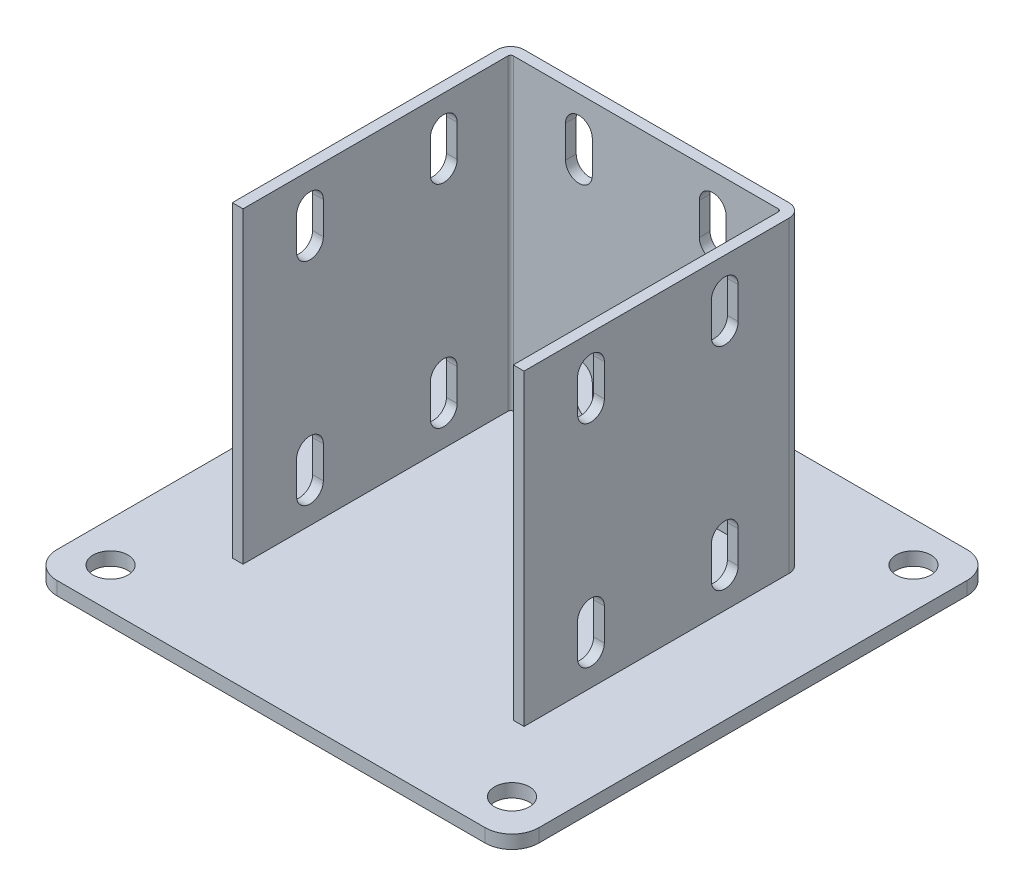
SolidWorks part; units mm, degrees
material "Ст3пс ГОСТ 380-2005"
ref_plane "Спереди" through (0, 0, 0) normal (0, 0, 1) x (1, 0, 0)
ref_plane "Сверху" through (0, 0, 0) normal (0, 1, 0) x (1, 0, 0)
ref_plane "Справа" through (0, 0, 0) normal (1, 0, 0) x (0, 0, -1)
sketch "Эскиз2" plane through (0, 0, 0) normal (0, 1, 0) x (1, 0, 0)
  line L1 (-90, -90) -> (90, -90)
  line L2 (-90, -90) -> (-90, 90)
  line L3 (-90, 90) -> (90, 90)
  line L4 (90, -90) -> (90, 90)
  line L5 (-90, -90) -> (90, 90) construction
  line L6 (-90, 90) -> (90, -90) construction
  point P0 (0, 0)
  dimension "D2" = 180
extrude "Бобышка-Вытянуть1" add sketch "Эскиз2" along normal blind 5
sketch "Эскиз3" plane through (0, 5, 0) normal (0, 1, 0) x (1, 0, 0)
  line L0 (-50.5, -50) -> (-50.5, 50)
  line L1 (-50.5, 50) -> (50.5, 50)
  line L2 (50.5, 50) -> (50.5, -50)
  point P2 (0, 50)
  point P5 (-50.5, 0)
  dimension "D2" = 101
  dimension "D3" = 100
extrude "Вытянуть-Тонкостенный1" add sketch "Эскиз3" along normal offset from surface (115 mm away) 120 thin up to face at (0, 0, 0) thin type one direction reverse wall 4
sketch "Эскиз4" plane through (0, 0, 0) normal (1, 0, 0) x (0, 0, -1)
  line L0 (54, 58.6936) -> (85, 5)
  line L1 (54, 120) -> (54, 5) construction
  line L2 (-90, 5) -> (90, 5) construction
  line L3 (85, 5) -> (54, 5)
  line L4 (54, 5) -> (54, 58.6936)
  line L5 (90, 5) -> (90, 0) construction
  dimension "D1" = 30
  dimension "D2" = 5
extrude "Бобышка-Вытянуть2" add sketch "Эскиз4" along normal mid plane 4
sketch "Эскиз5" plane through (54.5, 0, 0) normal (1, 0, 0) x (0, 0, -1)
  line L0 (-25, 108) -> (-25, 96) construction
  line L1 (-20, 108) -> (-20, 96)
  line L2 (-30, 108) -> (-30, 96)
  line L3 (-25, 29) -> (-25, 17) construction
  line L4 (-20, 29) -> (-20, 17)
  line L5 (-30, 29) -> (-30, 17)
  line L6 (-50, 120) -> (49, 120) construction
  line L7 (-90, 5) -> (90, 5) construction
  line L8 (0, 0) -> (0, 63.8564) construction
  line L11 (25, 108) -> (25, 96) construction
  line L14 (20, 108) -> (20, 96)
  line L15 (30, 108) -> (30, 96)
  line L16 (25, 29) -> (25, 17) construction
  line L17 (20, 29) -> (20, 17)
  line L18 (30, 29) -> (30, 17)
  arc A0 (-20, 108) -> (-30, 108) centre (-25, 108) ccw
  arc A1 (-30, 96) -> (-20, 96) centre (-25, 96) ccw
  arc A2 (-20, 29) -> (-30, 29) centre (-25, 29) ccw
  arc A3 (-30, 17) -> (-20, 17) centre (-25, 17) ccw
  arc A8 (20, 108) -> (30, 108) centre (25, 108) cw
  arc A9 (30, 96) -> (20, 96) centre (25, 96) cw
  arc A10 (20, 29) -> (30, 29) centre (25, 29) cw
  arc A11 (30, 17) -> (20, 17) centre (25, 17) cw
  point P3 (-25, 102)
  point P8 (-25, 23)
  point P22 (25, 102)
  point P29 (25, 23)
extrude "Вырез-Вытянуть1" cut sketch "Эскиз5" against normal through all
sketch "Эскиз6" plane through (0, 5, 0) normal (0, 1, 0) x (1, 0, 0)
  line L0 (-90, 90) -> (-90, -90) construction
  line L1 (75, -75) -> (-75, -75) construction
  line L2 (75, -75) -> (75, 75) construction
  line L3 (75, 75) -> (-75, 75) construction
  line L4 (-75, -75) -> (-75, 75) construction
  line L5 (75, -75) -> (-75, 75) construction
  line L6 (75, 75) -> (-75, -75) construction
  line L7 (90, 90) -> (-90, 90) construction
  circle A0 centre (-75, 75) radius 6.5
  circle A1 centre (-75, -75) radius 6.5
  circle A2 centre (75, 75) radius 6.5
  circle A3 centre (75, -75) radius 6.5
  point P0 (0, 0)
  dimension "D1" = 13
  dimension "D2" = 15
  dimension "D3" = 15
extrude "Вырез-Вытянуть2" cut sketch "Эскиз6" against normal through all
fillet "Скругление1" radius 10 4 edges at (90, 2.5, 90) (-90, 2.5, 90) (-90, 2.5, -90) (90, 2.5, -90)
sketch "Эскиз8" plane through (0, 0, -54) normal (0, 0, -1) x (-1, 0, 0)
  line L0 (-25, 108) -> (-25, 96) construction
  line L1 (-20, 108) -> (-20, 96)
  line L2 (-30, 108) -> (-30, 96)
  line L3 (-25, 29) -> (-25, 17) construction
  line L4 (-20, 29) -> (-20, 17)
  line L5 (-30, 29) -> (-30, 17)
  line L6 (-49.5, 120) -> (49.5, 120) construction
  line L7 (-80, 5) -> (80, 5) construction
  line L8 (0, 0) -> (0, 80) construction
  line L9 (-80, 0) -> (80, 0) construction
  line L10 (25, 108) -> (25, 96) construction
  line L11 (20, 108) -> (20, 96)
  line L12 (30, 108) -> (30, 96)
  line L13 (25, 29) -> (25, 17) construction
  line L14 (20, 29) -> (20, 17)
  line L15 (30, 29) -> (30, 17)
  arc A0 (-20, 108) -> (-30, 108) centre (-25, 108) ccw
  arc A1 (-30, 96) -> (-20, 96) centre (-25, 96) ccw
  arc A2 (-20, 29) -> (-30, 29) centre (-25, 29) ccw
  arc A3 (-30, 17) -> (-20, 17) centre (-25, 17) ccw
  arc A4 (20, 108) -> (30, 108) centre (25, 108) cw
  arc A5 (30, 96) -> (20, 96) centre (25, 96) cw
  arc A6 (20, 29) -> (30, 29) centre (25, 29) cw
  arc A7 (30, 17) -> (20, 17) centre (25, 17) cw
  point P2 (-25, 102)
  point P7 (-25, 23)
  point P24 (25, 102)
  point P31 (25, 23)
extrude "Вырез-Вытянуть3" cut sketch "Эскиз8" against normal up to next
equation "\"D5@Эскиз5\"=\"D5@Эскиз8\""
